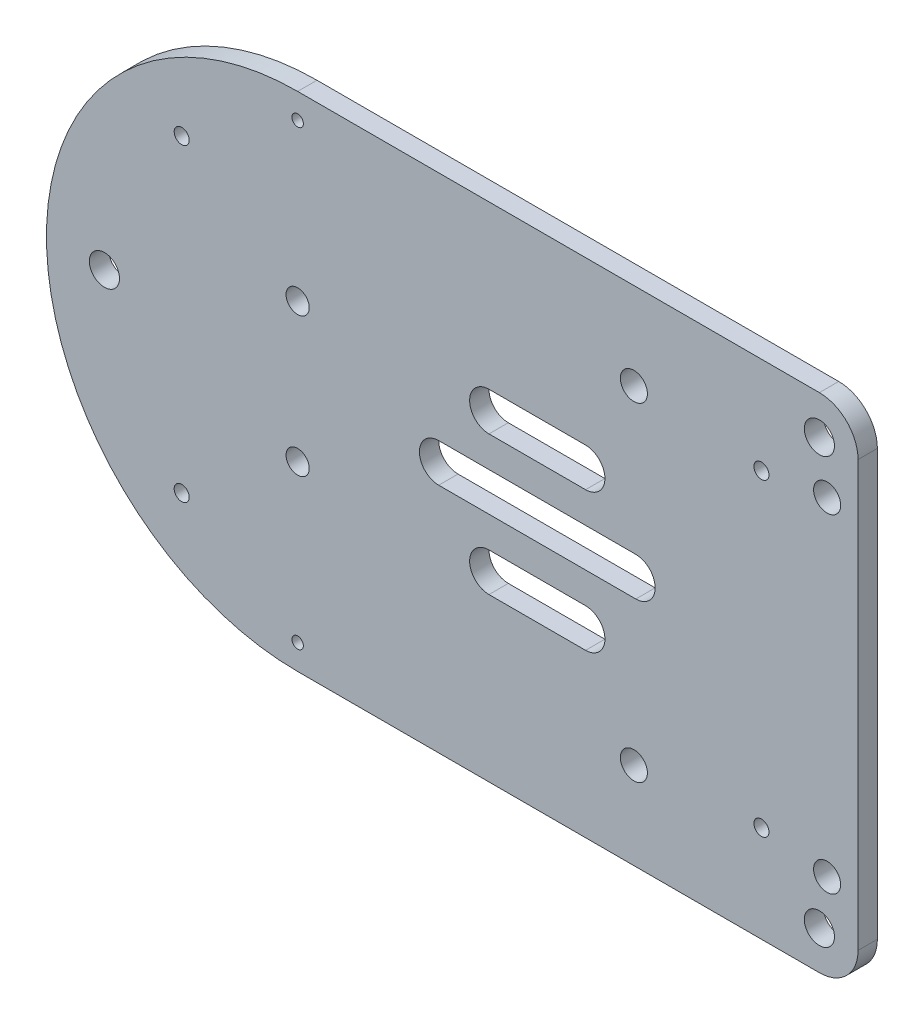
SolidWorks part; units mm, degrees
ref_plane "Front Plane" through (0, 0, 0) normal (0, 0, 1) x (1, 0, 0)
ref_plane "Top Plane" through (0, 0, 0) normal (0, 1, 0) x (1, 0, 0)
ref_plane "Right Plane" through (0, 0, 0) normal (1, 0, 0) x (0, 0, -1)
sketch "Sketch1" plane through (0, 0, 0) normal (0, 0, 1) x (1, 0, 0)
  line L0 (-105, 0) -> (105, 0) construction
  line L3 (-40, -65) -> (95, -65)
  line L4 (105, 55) -> (105, -55)
  line L5 (-40, 65) -> (95, 65)
  line L6 (80, 40) -> (-86.3432, 40) construction
  line L7 (-40, 81.3754) -> (-40, -121.1815) construction
  line L8 (-3.5, 0) -> (47.5, 0) construction
  line L9 (-3.5, 5) -> (47.5, 5)
  line L10 (-3.5, -5) -> (47.5, -5)
  line L11 (22, 0) -> (22, 36) construction
  line L12 (9.5, 18) -> (34.5, 18) construction
  line L13 (9.5, 23) -> (34.5, 23)
  line L14 (9.5, 13) -> (34.5, 13)
  line L15 (9.5, -18) -> (34.5, -18) construction
  line L16 (9.5, -23) -> (34.5, -23)
  line L17 (9.5, -13) -> (34.5, -13)
  circle A0 centre (95, 55) radius 3.9
  circle A1 centre (95, -55) radius 3.9
  arc A2 (-40, 65) -> (-40, -65) centre (-40, 0) ccw
  circle A3 centre (-90, 0) radius 3.9
  arc A4 (95, -65) -> (105, -55) centre (95, -55) ccw
  arc A5 (95, 65) -> (105, 55) centre (95, 55) cw
  circle A7 centre (-40, -18) radius 3
  circle A8 centre (-40, 18) radius 3
  circle A9 centre (80, 40) radius 1.95
  circle A10 centre (80, -40) radius 1.95
  circle A11 centre (-70, 40) radius 1.95
  circle A12 centre (-70, -40) radius 1.95
  circle A13 centre (47, 42.5) radius 3.5
  circle A14 centre (97, 42.5) radius 3.5
  circle A15 centre (97, -42.5) radius 3.5
  circle A16 centre (47, -42.5) radius 3.5
  arc A17 (-3.5, 5) -> (-3.5, -5) centre (-3.5, 0) ccw
  arc A18 (47.5, -5) -> (47.5, 5) centre (47.5, 0) ccw
  arc A19 (9.5, 23) -> (9.5, 13) centre (9.5, 18) ccw
  arc A20 (34.5, 13) -> (34.5, 23) centre (34.5, 18) ccw
  arc A21 (9.5, -23) -> (9.5, -13) centre (9.5, -18) cw
  arc A22 (34.5, -13) -> (34.5, -23) centre (34.5, -18) cw
  circle A23 centre (-40, 58.5) radius 1.475
  circle A24 centre (-40, -58.5) radius 1.475
  point P0 (0, 0)
  point P19 (105, -65)
  point P22 (105, 65)
  point P40 (22, 0)
  point P55 (22, 18)
  point P63 (22, -18)
  dimension "D3" = 7.8
  dimension "D7" = 65
  dimension "D6" = 40
  dimension "D8" = 50
  dimension "D4" = 105
  dimension "D5" = 10
  dimension "D9" = 110
  dimension "D10" = 6
  dimension "D11" = 3.9
  dimension "D14" = 3.9
  dimension "D19" = 7
  dimension "D20" = 7
  dimension "D25" = 5
  dimension "D26" = 5
  dimension "D29" = 2.95
  dimension "D1" = 65
  dimension "D2" = 65
  dimension "D12" = 25
  dimension "D13" = 25
  dimension "D15" = 150
  dimension "D16" = 36
  dimension "D17" = 42.5
  dimension "D18" = 58
  dimension "D21" = 42.5
  dimension "D22" = 8
  dimension "D23" = 36.5
  dimension "D24" = 51
  dimension "D27" = 25
  dimension "D28" = 8
  dimension "D30" = 6.5
extrude "Boss-Extrude2" add sketch "Sketch1" along normal blind 5
